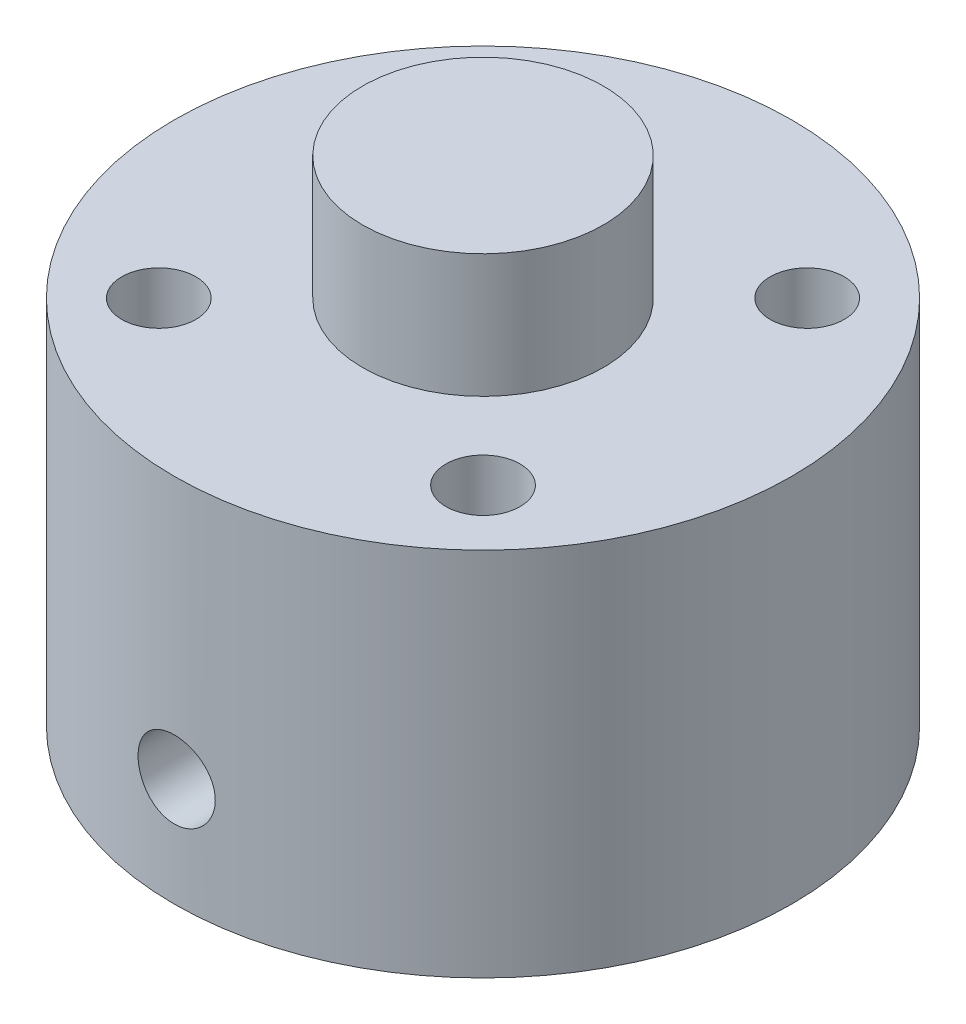
SolidWorks part; units mm, degrees
ref_plane "Ebene vorne" through (0, 0, 0) normal (0, 0, 1) x (1, 0, 0)
ref_plane "Ebene oben" through (0, 0, 0) normal (0, 1, 0) x (1, 0, 0)
ref_plane "Ebene rechts" through (0, 0, 0) normal (1, 0, 0) x (0, 0, -1)
sketch "Skizze1" plane through (0, 0, 0) normal (0, 1, 0) x (1, 0, 0)
  circle A0 centre (0, 0) radius 10
  dimension "D1" = 20
extrude "Aufsatz-Linear austragen1" add sketch "Skizze1" along normal blind 12
sketch "Skizze2" plane through (0, 12, 0) normal (0, 1, 0) x (1, 0, 0)
  circle A0 centre (0, 0) radius 3.9
  dimension "D1" = 7.8
extrude "Aufsatz-Linear austragen2" add sketch "Skizze2" along normal blind 4
sketch "Skizze3" plane through (0, 0, 0) normal (0, -1, 0) x (1, 0, 0)
  circle A0 centre (0, 0) radius 2.2
  dimension "D1" = 4.4
extrude "Schnitt-Linear austragen1" cut sketch "Skizze3" against normal blind 8
ref_plane "Ebene1" through (0, 0, 10) normal (0, 0, 1) x (1, 0, 0)
sketch "Skizze4" plane through (0, 0, 10) normal (0, 0, 1) x (1, 0, 0)
  line L0 (0, 0) -> (0, 12) construction
  line L1 (10, 12) -> (-10, 12) construction
  circle A0 centre (0, 3.5) radius 1.25
  dimension "D1" = 2.5
  dimension "D2" = 3.5
extrude "Schnitt-Linear austragen2" cut sketch "Skizze4" against normal up to next
sketch "Skizze5" plane through (0, 12, 0) normal (0, 1, 0) x (1, 0, 0)
  line L0 (0, 0) -> (-7.0711, 7.0711) construction
  line L1 (0, 0) -> (7.0711, 7.0711) construction
  line L2 (7.0711, 7.0711) -> (-7.0711, 7.0711) construction
  line L3 (-5.25, 5.25) -> (5.25, 5.25) construction
  line L4 (-10, 0) -> (10, 0) construction
  line L5 (-5.25, -5.25) -> (5.25, -5.25) construction
  line L6 (7.0711, -7.0711) -> (-7.0711, -7.0711) construction
  line L7 (0, 0) -> (7.0711, -7.0711) construction
  line L8 (0, 0) -> (-7.0711, -7.0711) construction
  line L9 (-5.25, 5.25) -> (-5.25, -5.25) construction
  circle A0 centre (0, 0) radius 10 construction
  circle A1 centre (-5.25, 5.25) radius 1.2
  circle A2 centre (5.25, 5.25) radius 1.2
  circle A3 centre (5.25, -5.25) radius 1.2
  circle A4 centre (-5.25, -5.25) radius 1.2
  dimension "D1" = 2.4
  dimension "D2" = 10.5
extrude "Schnitt-Linear austragen3" cut sketch "Skizze5" against normal blind 9
